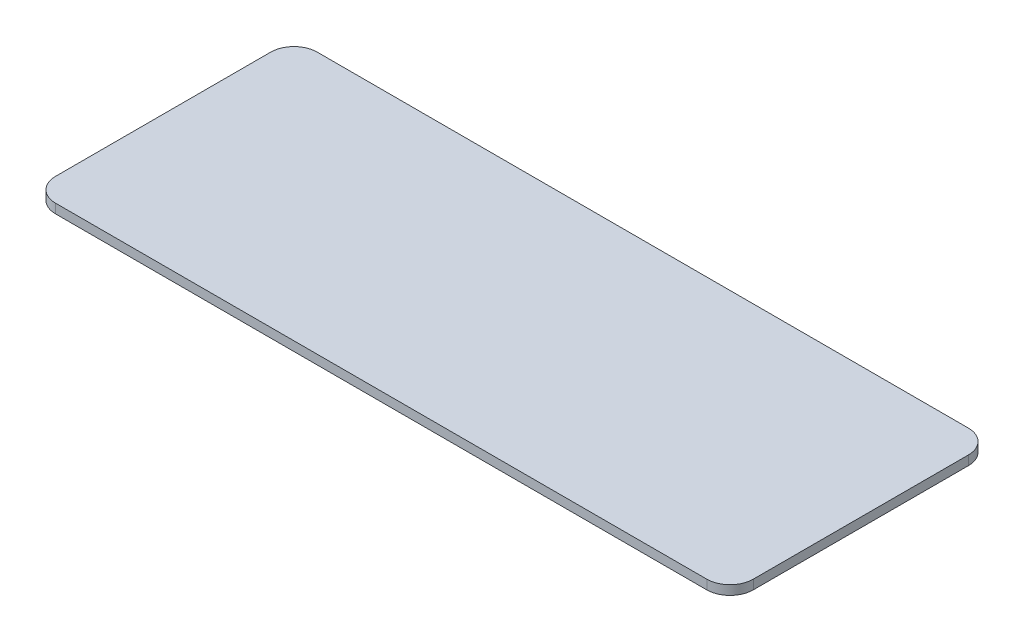
SolidWorks part; units mm, degrees
ref_plane "Front Plane" through (0, 0, 0) normal (0, 0, 1) x (1, 0, 0)
ref_plane "Top Plane" through (0, 0, 0) normal (0, 1, 0) x (1, 0, 0)
ref_plane "Right Plane" through (0, 0, 0) normal (1, 0, 0) x (0, 0, -1)
sketch "Sketch1" plane through (0, 0, 0) normal (0, 1, 0) x (1, 0, 0)
  line L1 (-60, -22.5) -> (60, -22.5)
  line L2 (-60, -22.5) -> (-60, 22.5)
  line L3 (-60, 22.5) -> (60, 22.5)
  line L4 (60, -22.5) -> (60, 22.5)
  line L5 (-60, -22.5) -> (60, 22.5) construction
  line L6 (-60, 22.5) -> (60, -22.5) construction
  point P0 (0, 0)
  dimension "D1" = 45
  dimension "D2" = 120
extrude "Boss-Extrude1" add sketch "Sketch1" along normal blind 1.6
fillet "Fillet1" radius 4 4 edges at (60, 0.8, 22.5) (60, 0.8, -22.5) (-60, 0.8, -22.5) (-60, 0.8, 22.5)
